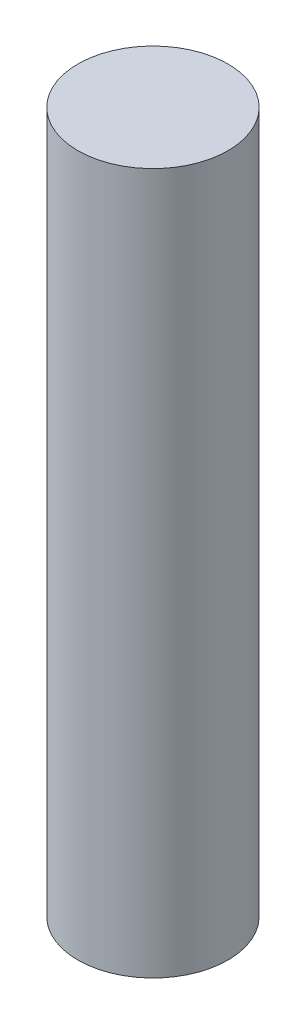
SolidWorks part; units mm, degrees
ref_plane "Front Plane" through (0, 0, 0) normal (0, 0, 1) x (1, 0, 0)
ref_plane "Top Plane" through (0, 0, 0) normal (0, 1, 0) x (1, 0, 0)
ref_plane "Right Plane" through (0, 0, 0) normal (1, 0, 0) x (0, 0, -1)
sketch "Sketch1" plane through (0, 0, 0) normal (0, 1, 0) x (1, 0, 0)
  circle A0 centre (0, 0) radius 7.5
extrude "Boss-Extrude1" add sketch "Sketch1" along normal blind 70
scale "Scale1" scale about origin uniform scaling yes scale factor 10
scale "Scale2" scale about centroid uniform scaling yes scale factor 0.75
